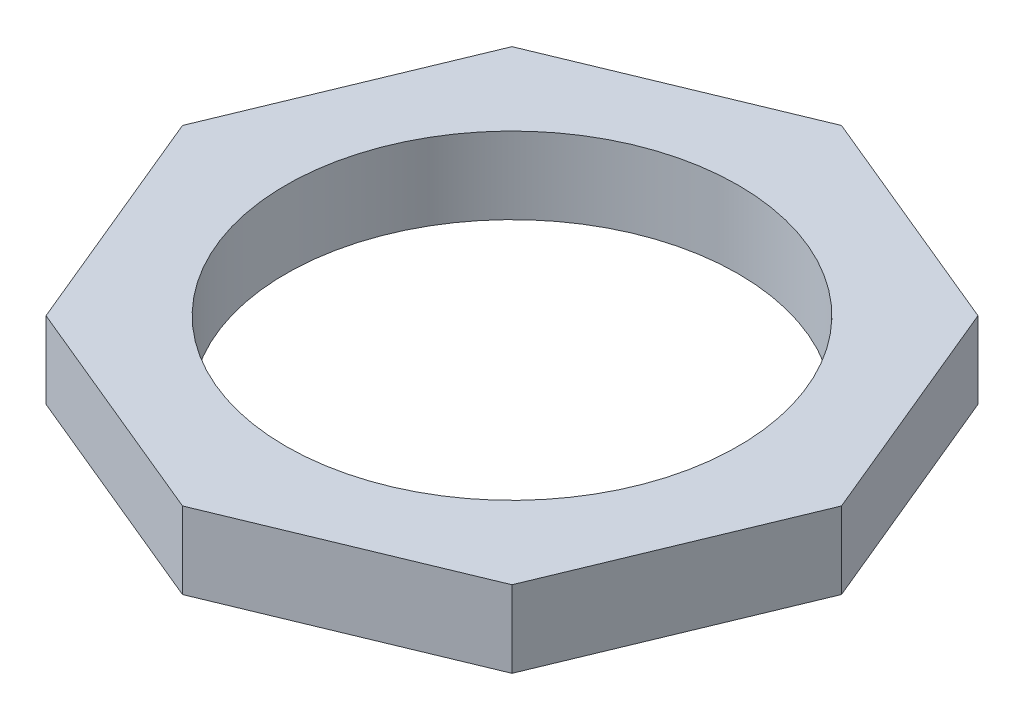
SolidWorks part; units mm, degrees
ref_plane "Front Plane" through (0, 0, 0) normal (0, 0, 1) x (1, 0, 0)
ref_plane "Top Plane" through (0, 0, 0) normal (0, 1, 0) x (1, 0, 0)
ref_plane "Right Plane" through (0, 0, 0) normal (1, 0, 0) x (0, 0, -1)
sketch "Sketch1" plane through (0, 0, 0) normal (0, 1, 0) x (1, 0, 0)
  line L0 (0, -57.9026) -> (43.4223, -39.9165)
  line L1 (61.4085, 3.5058) -> (43.4223, 46.9282)
  line L2 (43.4223, 46.9282) -> (0, 64.9143)
  line L3 (0, 64.9143) -> (-43.4223, 46.9282)
  line L4 (-43.4223, 46.9282) -> (-61.4085, 3.5058)
  line L5 (-61.4085, 3.5058) -> (-43.4223, -39.9165)
  line L6 (-43.4223, -39.9165) -> (0, -57.9026)
  line L7 (43.4223, -39.9165) -> (61.4085, 3.5058)
  circle A0 centre (0, 3.5058) radius 56.734 construction
  circle A1 centre (0, 3.5058) radius 42.15
  dimension "D1" = 47
extrude "Boss-Extrude2" add sketch "Sketch1" along normal blind 14.3
